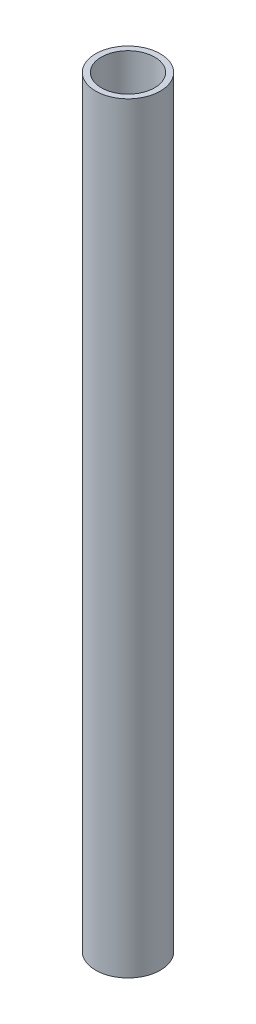
SolidWorks part; units mm, degrees
ref_plane "Спереди" through (0, 0, 0) normal (0, 0, 1) x (1, 0, 0)
ref_plane "Сверху" through (0, 0, 0) normal (0, 1, 0) x (1, 0, 0)
ref_plane "Справа" through (0, 0, 0) normal (1, 0, 0) x (0, 0, -1)
sketch "Эскиз1" plane through (0, 0, 0) normal (0, 1, 0) x (1, 0, 0)
  circle A0 centre (0, 0) radius 17
extrude "Вытянуть-Тонкостенный1" add sketch "Эскиз1" along normal blind 400 thin thin type one direction reverse wall 3
